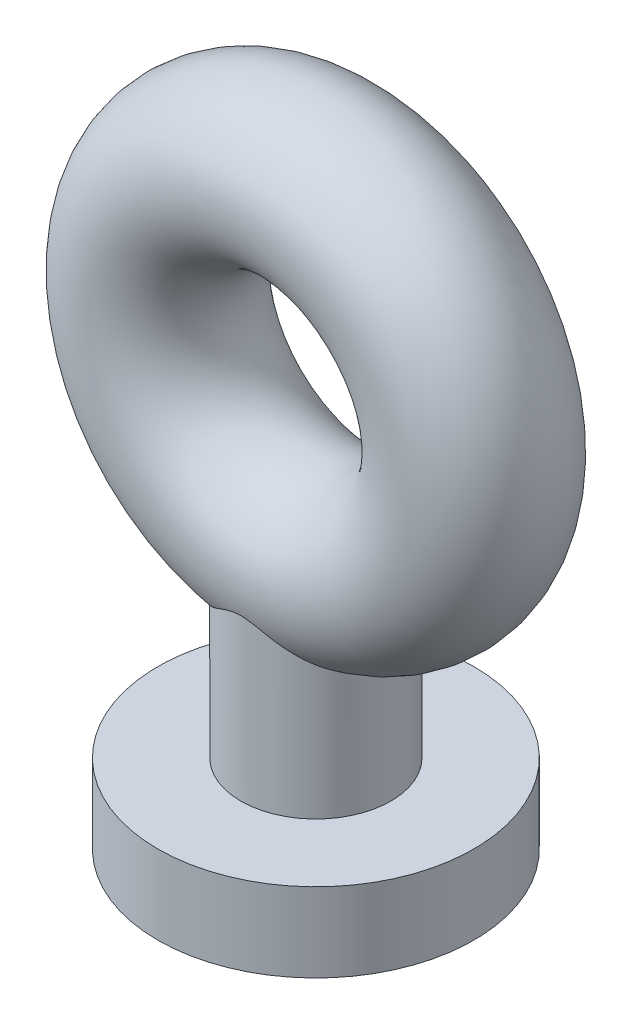
SolidWorks part; units mm, degrees
ref_plane "前视基准面" through (0, 0, 0) normal (0, 0, 1) x (1, 0, 0)
ref_plane "上视基准面" through (0, 0, 0) normal (0, 1, 0) x (1, 0, 0)
ref_plane "右视基准面" through (0, 0, 0) normal (1, 0, 0) x (0, 0, -1)
other "Configuration Table"
sketch "草图1" plane through (0, 0, 0) normal (0, 1, 0) x (1, 0, 0)
  line L0 (0, 0) -> (2, 0) construction
  line L1 (0, 0) -> (0, -0.6251) construction
  circle A0 centre (2, 0) radius 1
  dimension "D2" = 2
  dimension "D1" = 2
revolve "旋转1" add sketch "草图1" angle 360 about L1
sketch "草图2" plane through (0, 0, 0) normal (0, 0, 1) x (1, 0, 0)
  line L0 (0, 0) -> (0, -0.2915) construction
  line L1 (0, -1.8456) -> (0.95, -1.8456)
  line L2 (0.95, -1.8456) -> (0.95, -4.3456)
  line L3 (0.95, -4.3456) -> (2, -4.3456)
  line L4 (2, -4.3456) -> (2, -5.3456)
  line L5 (2, -5.3456) -> (0, -5.3456)
  line L6 (0, -5.3456) -> (0, -1.8456)
  circle A1 centre (0, 0) radius 3 construction
  point P10 (0.95, -2.8456)
  dimension "D5" = 1.5
  dimension "D1" = 0.95
  dimension "D2" = 1
  dimension "D3" = 2.5
  dimension "D4" = 2
revolve "旋转2" add sketch "草图2" angle 360 about L0
